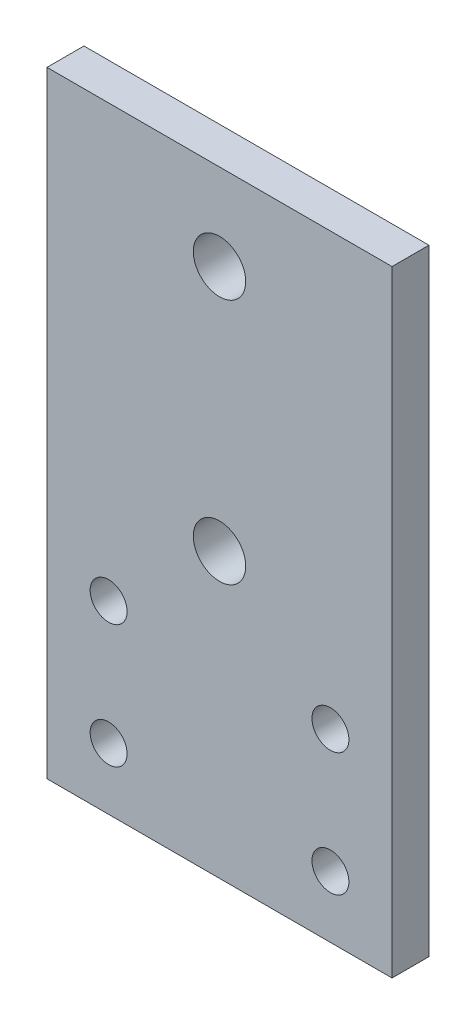
SolidWorks part; units mm, degrees
ref_plane "Plano frontal" through (0, 0, 0) normal (0, 0, 1) x (1, 0, 0)
ref_plane "Plano superior" through (0, 0, 0) normal (0, 1, 0) x (1, 0, 0)
ref_plane "Plano direito" through (0, 0, 0) normal (1, 0, 0) x (0, 0, -1)
sketch "Esboço1" plane through (0, 0, 0) normal (0, 0, 1) x (1, 0, 0)
  line L0 (0, 25) -> (0, 18) construction
  line L1 (-14, -25) -> (14, -25)
  line L2 (-14, -25) -> (-14, 25)
  line L3 (-14, 25) -> (14, 25)
  line L4 (14, -25) -> (14, 25)
  line L5 (-14, -25) -> (14, 25) construction
  line L7 (0, 18) -> (0, -2) construction
  line L8 (-9, -25) -> (-9, -20) construction
  line L9 (-9, -20) -> (-9, -10) construction
  line L10 (9, -20) -> (9, -10) construction
  line L11 (9, -25) -> (9, -20) construction
  line L12 (14, -25) -> (-14, 25) construction
  circle A0 centre (0, 18) radius 2.125
  circle A1 centre (0, -2) radius 2.125
  circle A2 centre (-9, -10) radius 1.5
  circle A3 centre (-9, -20) radius 1.5
  circle A4 centre (9, -20) radius 1.5
  circle A5 centre (9, -10) radius 1.5
  point P0 (0, 0)
  dimension "D3" = 4.25
  dimension "D9" = 3
  dimension "D1" = 28
  dimension "D2" = 50
  dimension "D4" = 7
  dimension "D5" = 20
  dimension "D6" = 5
  dimension "D7" = 10
  dimension "D8" = 5
extrude "Ressalto-extrusão1" add sketch "Esboço1" along normal blind 3
